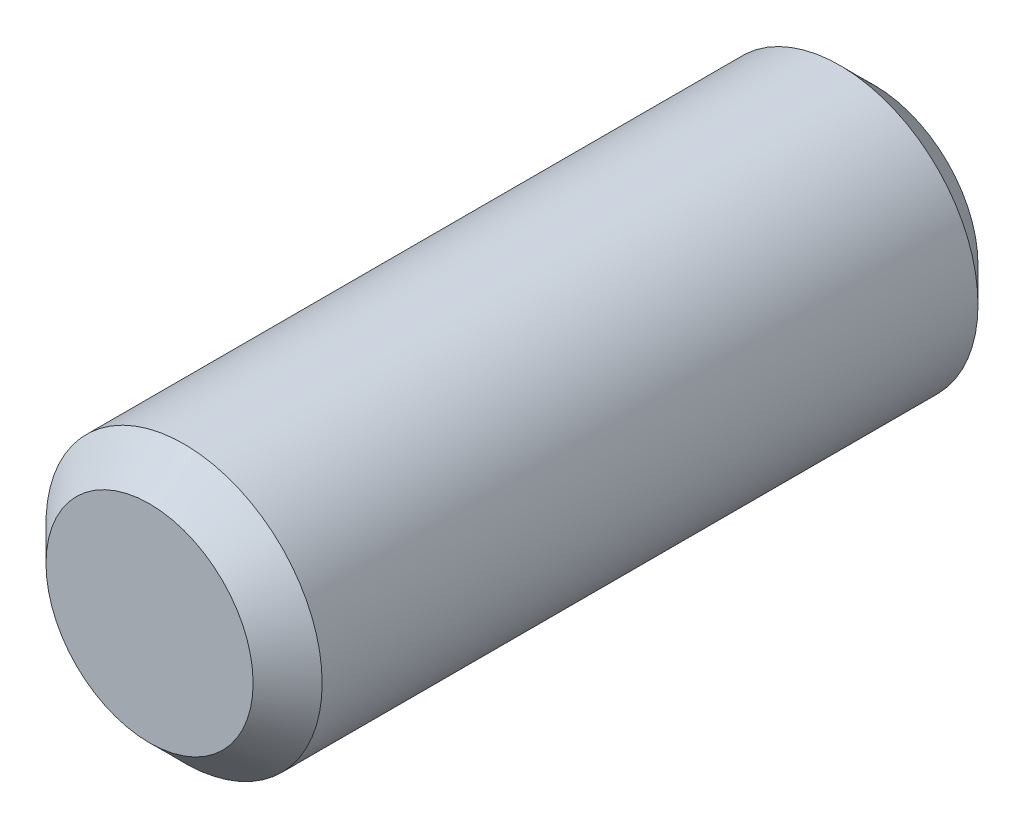
SolidWorks part; units mm, degrees
ref_plane "Front Plane" through (0, 0, 0) normal (0, 0, 1) x (1, 0, 0)
ref_plane "Top Plane" through (0, 0, 0) normal (0, 1, 0) x (1, 0, 0)
ref_plane "Right Plane" through (0, 0, 0) normal (1, 0, 0) x (0, 0, -1)
sketch "Sketch1" plane through (0, 0, 0) normal (0, 0, 1) x (1, 0, 0)
  circle A0 centre (0, 0) radius 4
  dimension "D1" = 8
extrude "Boss-Extrude1" add sketch "Sketch1" along normal blind 21
chamfer "Chamfer1" distance 1 angle 45 2 edges at (4, 0, 0) (4, 0, 21)
